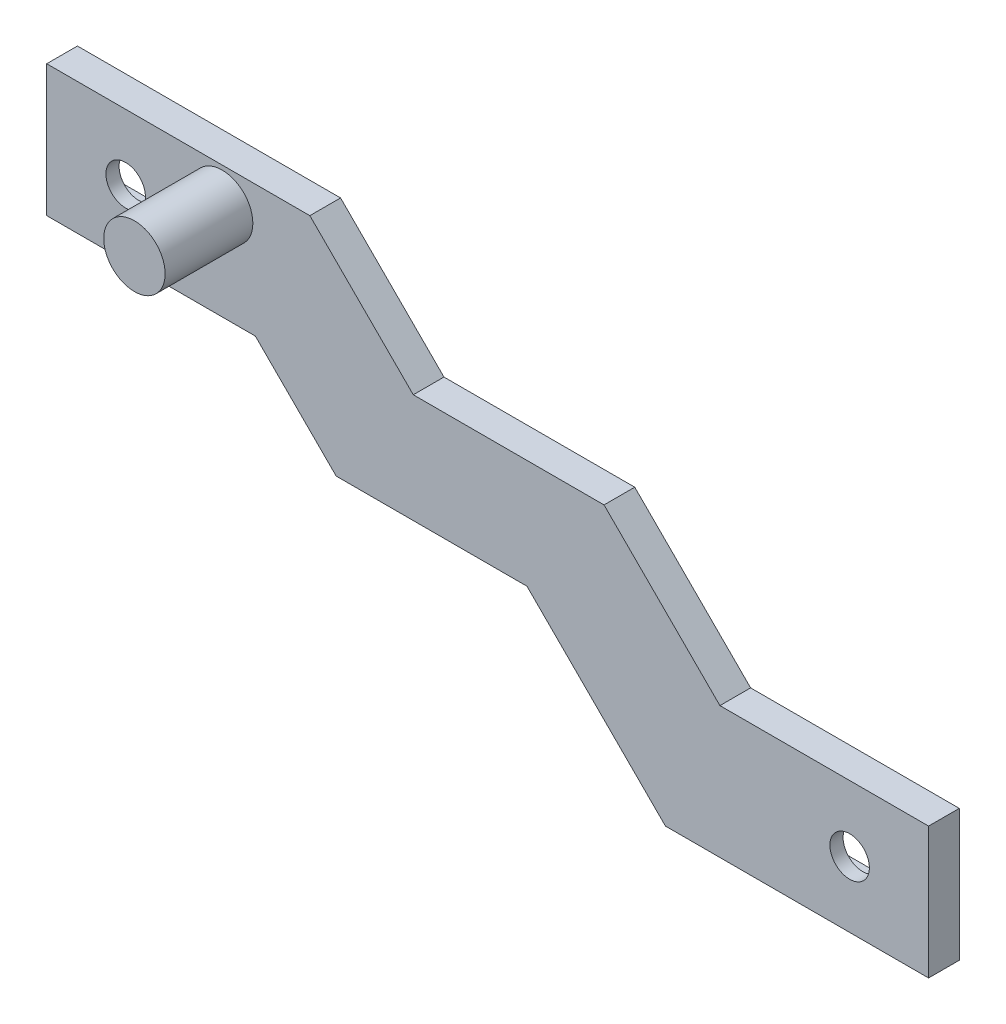
SolidWorks part; units mm, degrees
ref_plane "Спереди" through (0, 0, 0) normal (0, 0, 1) x (1, 0, 0)
ref_plane "Сверху" through (0, 0, 0) normal (0, 1, 0) x (1, 0, 0)
ref_plane "Справа" through (0, 0, 0) normal (1, 0, 0) x (0, 0, -1)
sketch "Эскиз1" plane through (0, 0, 0) normal (0, 0, 1) x (1, 0, 0)
  line L1 (112.7696, -7.5) -> (12.2304, -7.5)
  line L2 (112.7696, -7.5) -> (112.7696, 32.5)
  line L3 (112.7696, 32.5) -> (12.2304, 32.5)
  line L4 (12.2304, -7.5) -> (12.2304, 32.5)
  line L9 (32.7304, 21.5) -> (15.7304, 21.5)
  line L10 (32.7304, 21.5) -> (32.7304, 28.5)
  line L11 (32.7304, 28.5) -> (15.7304, 28.5)
  line L12 (15.7304, 21.5) -> (15.7304, 28.5)
  line L14 (16.2304, 22) -> (32.2304, 22) construction
  line L17 (50.7696, -3.5) -> (110.7696, -3.5) construction
  line L20 (110.7696, 3.5) -> (50.7696, 3.5) construction
  line L21 (109.2696, -3.5) -> (92.2696, -3.5)
  line L22 (109.2696, -3.5) -> (109.2696, 3.5)
  line L23 (109.2696, 3.5) -> (92.2696, 3.5)
  line L24 (92.2696, -3.5) -> (92.2696, 3.5)
  line L25 (108.7696, -3) -> (108.7696, 3) construction
  line L26 (92.7696, 3) -> (92.7696, -3) construction
  dimension "D1" = 0.5
  dimension "D2" = 17
  dimension "D3" = 7
  dimension "D4" = 0.5
  dimension "D5" = 0.5
extrude "Бобышка-Вытянуть1" add sketch "Эскиз1" along normal blind 2
sketch "Эскиз2" plane through (0, 0, 2) normal (0, 0, 1) x (1, 0, 0)
  line L1 (12.2304, 32.5) -> (112.7696, 32.5)
  line L2 (12.2304, 32.5) -> (12.2304, -7.5)
  line L3 (12.2304, -7.5) -> (112.7696, -7.5)
  line L4 (112.7696, 32.5) -> (112.7696, -7.5)
  circle A0 centre (21.2304, 25) radius 2.25
  circle A1 centre (103.7696, 0) radius 2.25
extrude "Бобышка-Вытянуть2" add sketch "Эскиз2" along normal blind 1.5
sketch "Эскиз3" plane through (0, 0, 3.5) normal (0, 0, 1) x (1, 0, 0)
  line L0 (12.2304, 32.5) -> (42.2304, 32.5)
  line L1 (112.7696, 32.5) -> (12.2304, 32.5) construction
  line L2 (42.2304, 32.5) -> (54.0204, 20.71)
  line L3 (54.0204, 20.71) -> (75.7696, 20.71)
  line L4 (75.7696, 20.71) -> (88.9796, 7.5)
  line L5 (88.9796, 7.5) -> (112.7696, 7.5)
  line L6 (112.7696, -7.5) -> (112.7696, 32.5) construction
  line L7 (112.7696, 7.5) -> (112.7696, -7.5)
  line L8 (112.7696, -7.5) -> (82.7696, -7.5)
  line L9 (12.2304, -7.5) -> (112.7696, -7.5) construction
  line L10 (82.7696, -7.5) -> (66.9828, 8.2868)
  line L11 (66.9828, 8.2868) -> (45.2304, 8.2868)
  line L12 (45.2304, 8.2868) -> (36.0172, 17.5)
  line L13 (36.0172, 17.5) -> (12.2304, 17.5)
  line L14 (12.2304, 32.5) -> (12.2304, -7.5) construction
  line L15 (12.2304, 17.5) -> (12.2304, 32.5)
  line L17 (-11.173, 55.2443) -> (173.6359, 55.2443)
  line L18 (-11.173, 55.2443) -> (-11.173, -39.5809)
  line L19 (-11.173, -39.5809) -> (173.6359, -39.5809)
  line L20 (173.6359, 55.2443) -> (173.6359, -39.5809)
  circle A0 centre (103.7696, 0) radius 1.25 construction
  circle A1 centre (21.2304, 25) radius 1.25 construction
  dimension "D4" = 7.5
  dimension "D1" = 45
  dimension "D2" = 45
  dimension "D3" = 7.5
  dimension "D5" = 7.5
  dimension "D6" = 45
  dimension "D7" = 15
  dimension "D8" = 30
  dimension "D9" = 30
  dimension "D10" = 23.7868
  dimension "D11" = 23.79
  dimension "D12" = 14.9977
  dimension "D13" = 33
  dimension "D14" = 37
extrude "Вырез-Вытянуть1" cut sketch "Эскиз3" against normal blind 31.5
sketch "Эскиз4" plane through (0, 0, 3.5) normal (0, 0, 1) x (1, 0, 0)
  line L1 (42.2304, 32.5) -> (12.2304, 32.5) construction
  line L3 (12.2304, 32.5) -> (12.2304, 17.5) construction
  circle A0 centre (32.2304, 28.5) radius 3.5
  point P5 (21.2304, 25)
  dimension "D1" = 7
  dimension "D3" = 20
  dimension "D2" = 4
extrude "Бобышка-Вытянуть3" add sketch "Эскиз4" along normal blind 10
